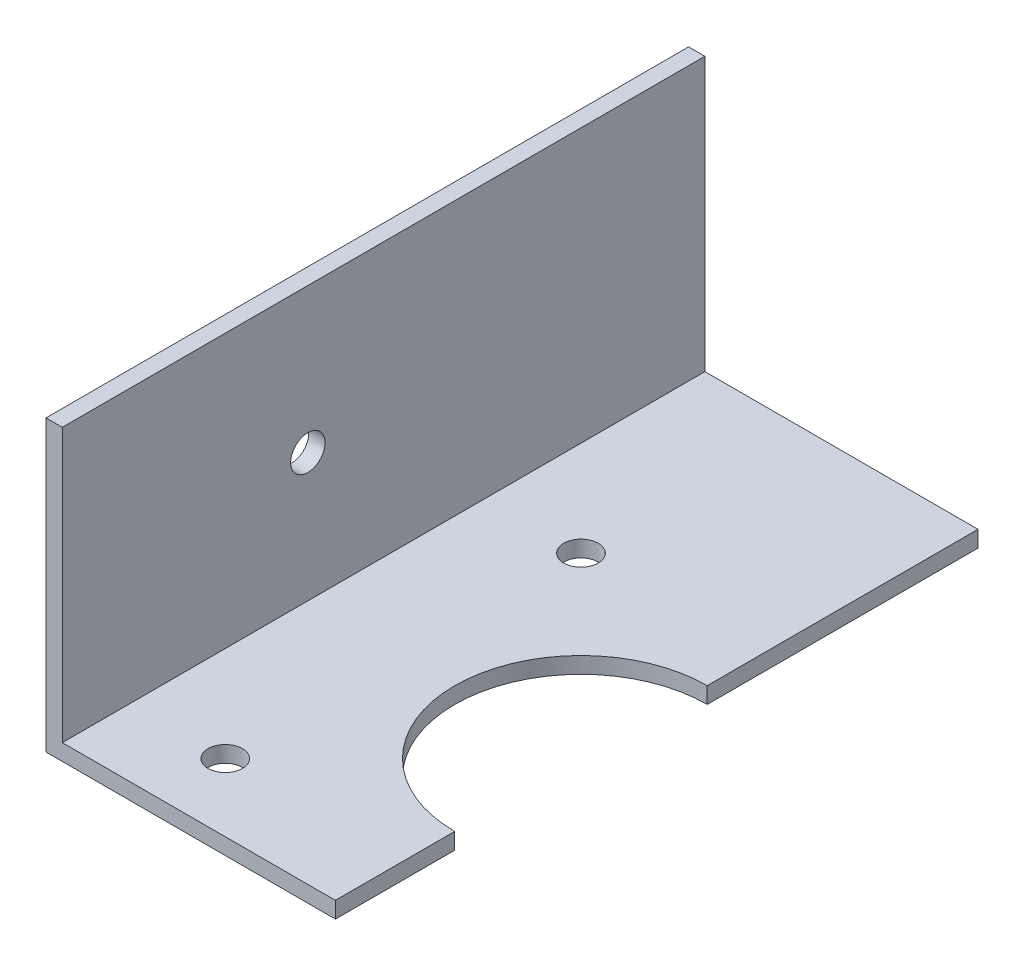
SolidWorks part; units mm, degrees
ref_plane "Front" through (0, 0, 0) normal (0, 0, 1) x (1, 0, 0)
ref_plane "Top" through (0, 0, 0) normal (0, 1, 0) x (1, 0, 0)
ref_plane "Right" through (0, 0, 0) normal (1, 0, 0) x (0, 0, -1)
sketch "Sketch1" plane through (0, 0, 0) normal (0, 0, 1) x (1, 0, 0)
  line L0 (0, 0) -> (0, -25.22)
  line L1 (25.22, -25.22) -> (0, -25.22)
  line L2 (25.22, -25.22) -> (25.22, -23.8)
  line L3 (25.22, -23.8) -> (1.42, -23.8)
  line L4 (1.42, 0) -> (1.42, -23.8)
  line L5 (1.42, 0) -> (0, 0)
extrude "Extrude1" add sketch "Sketch1" along normal blind 56
sketch "Sketch2" plane through (0, 0, 0) normal (-1, 0, 0) x (0, 0, 1)
  circle A0 centre (34.6, -12.61) radius 1.5
extrude "Cut-Extrude1" cut sketch "Sketch2" against normal through all
sketch "Sketch3" plane through (0, -25.22, 0) normal (0, -1, 0) x (1, 0, 0)
  line L0 (25.22, 56) -> (25.22, 0) construction
  circle A0 centre (25.22, 34.6) radius 11
extrude "Cut-Extrude2" cut sketch "Sketch3" against normal through all
sketch "Sketch4" plane through (0, -25.22, 0) normal (0, -1, 0) x (1, 0, 0)
  circle A0 centre (9.72, 19.1) radius 1.5
extrude "Cut-Extrude3" cut sketch "Sketch4" against normal through all
sketch "Sketch5" plane through (0, -25.22, 0) normal (0, -1, 0) x (1, 0, 0)
  circle A0 centre (9.72, 50.1) radius 1.5
extrude "Cut-Extrude4" cut sketch "Sketch5" against normal through all
